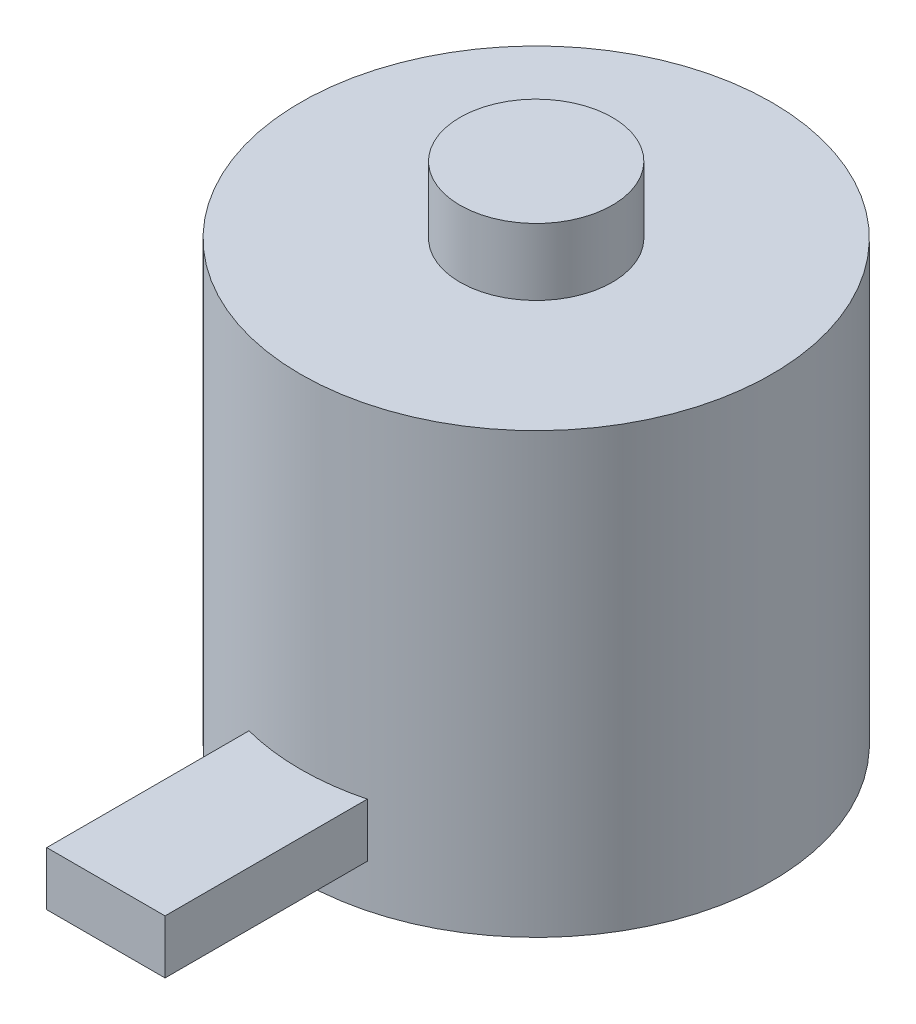
SolidWorks part; units mm, degrees
ref_plane "Front Plane" through (0, 0, 0) normal (0, 0, 1) x (1, 0, 0)
ref_plane "Top Plane" through (0, 0, 0) normal (0, 1, 0) x (1, 0, 0)
ref_plane "Right Plane" through (0, 0, 0) normal (1, 0, 0) x (0, 0, -1)
other "Bounding Box"
ref_plane "Default Plane" through (13.8565, 3.175, 6.7999) normal (0, -1, 0) x (-1, 0, 0)
sketch "Sketch1" plane through (0, 0, 0) normal (0, 1, 0) x (1, 0, 0)
  circle A0 centre (0, 0) radius 13.9065
  dimension "D1" = 27.813
extrude "Boss-Extrude1" add sketch "Sketch1" along normal mid plane 29.845
sketch "Sketch2" plane through (0, 14.9225, 0) normal (0, 1, 0) x (1, 0, 0)
  circle A0 centre (0, 0) radius 4.4958
  circle A1 centre (0, 0) radius 13.9065
  circle A2 centre (0, 0) radius 13.9065 construction
  dimension "D1" = 8.9916
extrude "Cut-Extrude1" cut sketch "Sketch2" against normal offset from surface (3.937 mm away) 25.908 up to face at (0, -14.9225, 13.9065)
sketch "Sketch3" plane through (0, 0, 0) normal (0, 0, 1) x (1, 0, 0)
  line L1 (-3.4925, -12.3825) -> (3.4925, -12.3825)
  line L2 (-3.4925, -12.3825) -> (-3.4925, -9.2075)
  line L3 (-3.4925, -9.2075) -> (3.4925, -9.2075)
  line L4 (3.4925, -12.3825) -> (3.4925, -9.2075)
  line L5 (-3.4925, -12.3825) -> (3.4925, -9.2075) construction
  line L6 (-3.4925, -9.2075) -> (3.4925, -12.3825) construction
  line L7 (-13.9065, -14.9225) -> (13.9065, -14.9225) construction
  point P0 (0, -10.795)
  point P5 (0, 0)
  point P7 (-5.8012, -14.9225)
  point P8 (0, -10.9341)
  dimension "D1" = 3.175
  dimension "D2" = 2.54
  dimension "D3" = 6.985
extrude "Boss-Extrude2" add sketch "Sketch3" along normal blind 25.4
sketch "Sketch4" plane through (0, -14.9225, 0) normal (0, -1, 0) x (1, 0, 0)
  line L0 (-6.7175, -6.7175) -> (6.7175, 6.7175) construction
  line L1 (-5.6569, 5.6569) -> (5.6569, -5.6569) construction
  line L2 (-3.4925, 25.4) -> (-3.4925, 13.4608) construction
  circle A0 centre (-5.6569, 5.6569) radius 1.5
  circle A1 centre (6.7175, 6.7175) radius 1.5
  circle A2 centre (5.6569, -5.6569) radius 1.5
  circle A3 centre (-6.7175, -6.7175) radius 1.5
  point P4 (0, 0)
  point P5 (0, 0)
  dimension "D2" = 3
  dimension "D1" = 45
  dimension "D3" = 16
  dimension "D4" = 19
extrude "Cut-Extrude2" cut sketch "Sketch4" against normal blind 12.7
